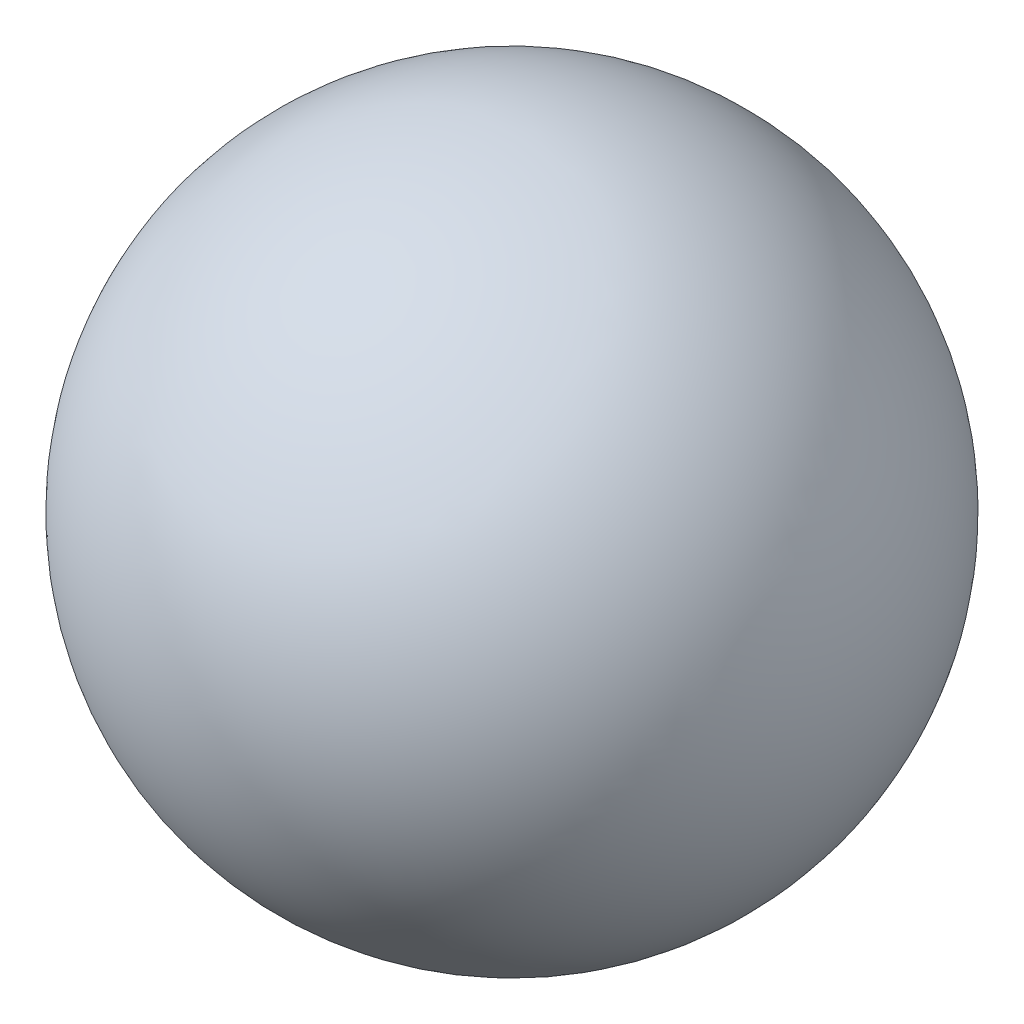
SolidWorks part; units mm, degrees
ref_plane "Front Plane" through (0, 0, 0) normal (0, 0, 1) x (1, 0, 0)
ref_plane "Top Plane" through (0, 0, 0) normal (0, 1, 0) x (1, 0, 0)
ref_plane "Right Plane" through (0, 0, 0) normal (1, 0, 0) x (0, 0, -1)
ref_plane "Plane1" through (0, 0, 0) normal (0, 0, 1) x (1, 0, 0)
sketch "Sketch1" plane through (0, 0, 0) normal (0, 0, 1) x (1, 0, 0)
  line L0 (0.8, 1) -> (0.2, 1)
  line L1 (0.8, 1) -> (0.2, 1) construction
  arc A0 (0.2, 1) -> (0.8, 1) centre (0.5, 1) cw
revolve "Revolve1" add sketch "Sketch1" angle 360 about L1
